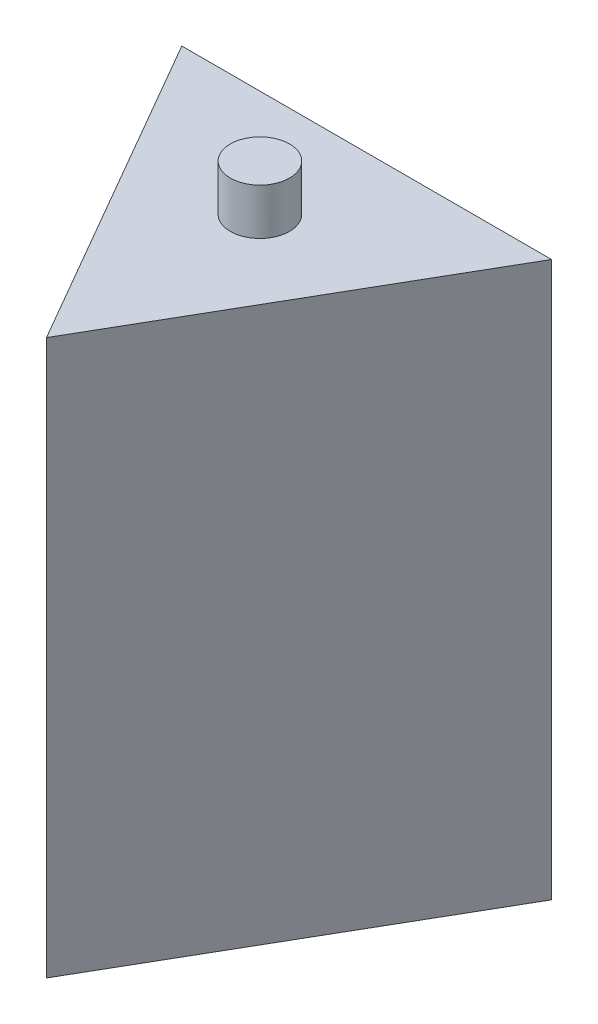
SolidWorks part; units mm, degrees
ref_plane "Front Plane" through (0, 0, 0) normal (0, 0, 1) x (1, 0, 0)
ref_plane "Top Plane" through (0, 0, 0) normal (0, 1, 0) x (1, 0, 0)
ref_plane "Right Plane" through (0, 0, 0) normal (1, 0, 0) x (0, 0, -1)
sketch "Sketch1" plane through (0, 0, 0) normal (0, 1, 0) x (1, 0, 0)
  line L0 (0, 0) -> (-25.4, 43.9941)
  line L1 (-25.4, 43.9941) -> (25.4, 43.9941)
  line L2 (25.4, 43.9941) -> (0, 0)
  dimension "D1" = 50.8
extrude "Boss-Extrude1" add sketch "Sketch1" along normal blind 76.2
sketch "Sketch2" plane through (0, 0, 0) normal (0, 1, 0) x (1, 0, 0)
  line L0 (0, 87.9882) -> (0, 0) construction
  line L2 (-12.7, 21.997) -> (25.4, 43.9941) construction
  line L3 (-25.4, 43.9941) -> (0, 0) construction
  line L5 (12.7, 26.1544) -> (-12.7, 26.1544)
  line L6 (12.7, 26.1544) -> (12.7, 32.5044)
  line L7 (12.7, 32.5044) -> (-12.7, 32.5044)
  line L8 (-12.7, 26.1544) -> (-12.7, 32.5044)
  line L9 (12.7, 26.1544) -> (-12.7, 32.5044) construction
  line L10 (12.7, 32.5044) -> (-12.7, 26.1544) construction
  point P3 (0, 43.9941)
  point P9 (0, 29.3294)
  dimension "D1" = 6.35
  dimension "D2" = 25.4
ref_plane "Plane1" through (0, 76.2, 0) normal (0, 1, 0) x (1, 0, 0)
sketch "Sketch3" plane through (0, 76.2, 0) normal (0, 1, 0) x (1, 0, 0)
  line L0 (0, 43.9941) -> (0, 0) construction
  line L1 (25.4, 43.9941) -> (-25.4, 43.9941) construction
  line L2 (25.4, 43.9941) -> (-12.7, 21.997) construction
  line L3 (-25.4, 43.9941) -> (0, 0) construction
  circle A0 centre (0, 29.3294) radius 4.064
  dimension "D1" = 8.128
extrude "Boss-Extrude2" add sketch "Sketch3" along normal blind 6.35 contours A0
extrude "Cut-Extrude2" cut sketch "Sketch2" along normal blind 25.4
